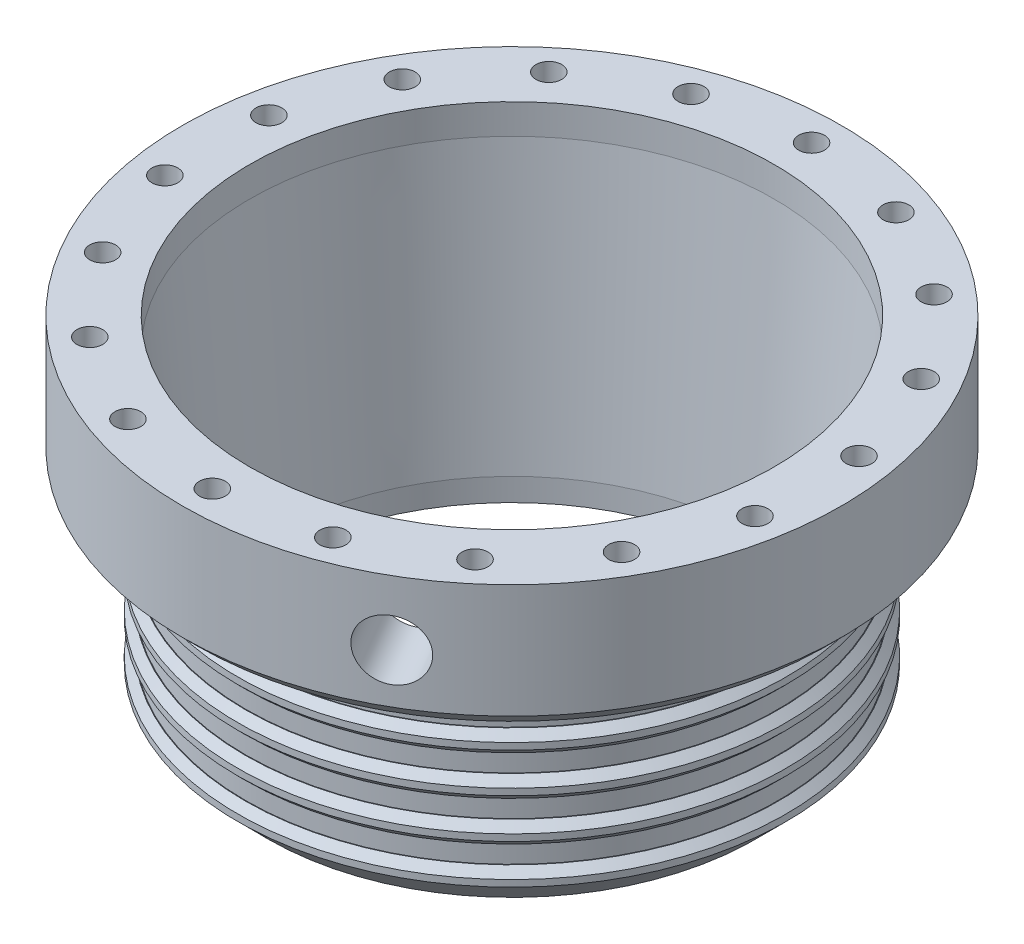
SolidWorks part; units mm, degrees
material "6061-T4 (SS)"
ref_plane "Front Plane" through (0, 0, 0) normal (0, 0, 1) x (1, 0, 0)
ref_plane "Top Plane" through (0, 0, 0) normal (0, 1, 0) x (1, 0, 0)
ref_plane "Right Plane" through (0, 0, 0) normal (1, 0, 0) x (0, 0, -1)
sketch "Sketch1" plane through (0, 0, 0) normal (0, 1, 0) x (1, 0, 0)
  circle A0 centre (0, 0) radius 55.5625
  circle A1 centre (0, 0) radius 58.1025
  dimension "D1" = 111.125
  dimension "D2" = 2.54
extrude "Boss-Extrude1" add sketch "Sketch1" along normal blind 38.1
sketch "Sketch2" plane through (0, 38.1, 0) normal (0, 1, 0) x (1, 0, 0)
  circle A0 centre (0, 0) radius 55.5625
  circle A1 centre (0, 0) radius 69.85
  circle A2 centre (0, 0) radius 55.5625 construction
  dimension "D1" = 139.7
extrude "Boss-Extrude2" add sketch "Sketch2" along normal blind 20.955
sketch "Sketch7" plane through (0, 0, 0) normal (0, 0, 1) x (1, 0, 0)
  line L0 (0, 0) -> (0, 88.9) construction
ref_plane "Plane1" through (0, 0, 0) normal (0.9659, 0, -0.2588) x (0, 1, 0)
ref_plane "Plane2" through (18.0785, 0, 67.4699) normal (0.2588, 0, 0.9659) x (0.9659, 0, -0.2588)
sketch "Sketch9" plane through (0, 0, 0) normal (0, 0, 1) x (1, 0, 0)
  line L0 (0, 0) -> (0, 88.9) construction
  line L2 (0, 0) -> (-58.1025, 0) construction
  line L3 (-58.1025, 0) -> (58.1025, 0) construction
  line L4 (-58.1025, 0) -> (-58.1025, 38.1) construction
  line L5 (-69.85, 38.1) -> (69.85, 38.1) construction
  line L6 (-58.1025, 38.1) -> (58.1025, 38.1) construction
  line L7 (-58.1025, 38.1) -> (-58.1025, 33.528)
  line L8 (-58.1025, 4.572) -> (-56.388, 4.572)
  line L9 (-58.1025, 4.572) -> (-58.1025, 8.382)
  line L10 (-58.1025, 8.382) -> (-56.388, 8.382)
  line L11 (-56.388, 4.572) -> (-56.388, 8.382)
  line L12 (-58.1025, 12.954) -> (-56.388, 12.954)
  line L13 (-58.1025, 12.954) -> (-58.1025, 16.764)
  line L14 (-58.1025, 16.764) -> (-56.388, 16.764)
  line L15 (-56.388, 12.954) -> (-56.388, 16.764)
  line L16 (-58.1025, 21.336) -> (-56.388, 21.336)
  line L17 (-58.1025, 21.336) -> (-58.1025, 25.146)
  line L18 (-58.1025, 25.146) -> (-56.388, 25.146)
  line L19 (-56.388, 21.336) -> (-56.388, 25.146)
  line L20 (-58.1025, 29.718) -> (-56.388, 29.718)
  line L21 (-58.1025, 29.718) -> (-58.1025, 33.528)
  line L22 (-58.1025, 33.528) -> (-56.388, 33.528)
  line L23 (-56.388, 29.718) -> (-56.388, 33.528)
  line L24 (-58.1025, 29.718) -> (-58.1025, 25.146)
  line L25 (-58.1025, 21.336) -> (-58.1025, 16.764)
  line L26 (-58.1025, 12.954) -> (-58.1025, 8.382)
  line L27 (-58.1025, 4.572) -> (-58.1025, 0)
  dimension "D1" = 58.1025
  dimension "D2" = 1.7145
  dimension "D3" = 3.81
revolve "Cut-Revolve1" cut sketch "Sketch9" angle 360 about L0
chamfer "Chamfer1" distance 1.5875 angle 45 1 edges at (0, 0, 58.1025)
sketch "Sketch10" plane through (0, 0, 0) normal (0, 0, 1) x (1, 0, 0)
  line L0 (0, 0) -> (0, 88.7441) construction
  line L1 (0, 0) -> (55.5625, 0) construction
  line L2 (55.5625, 0) -> (55.5625, 59.055)
  line L3 (55.5625, 59.055) -> (50.8, 0)
  line L4 (50.8, 0) -> (55.5625, 0)
  dimension "D1" = 55.5625
  dimension "D2" = 59.055
  dimension "D3" = 50.8
revolve "Revolve1" add sketch "Sketch10" angle 360 about L0
sketch "Sketch16" plane through (0, 59.055, 0) normal (0, 1, 0) x (1, 0, 0)
  circle A0 centre (0, 0) radius 69.85
  circle A1 centre (0, 0) radius 55.5625
  circle A3 centre (0, 0) radius 69.85 construction
  circle A5 centre (0, 0) radius 55.5625 construction
extrude "Boss-Extrude3" add sketch "Sketch16" along normal blind 6.35
sketch "Sketch11" plane through (0, 65.405, 0) normal (0, 1, 0) x (1, 0, 0)
  circle A0 centre (0, 0) radius 61.9633
  circle A1 centre (0, 0) radius 59.3217
  dimension "D1" = 123.9266
  dimension "D2" = 2.6416
sketch "Sketch12" plane through (0, 65.405, 0) normal (0, 1, 0) x (1, 0, 0)
  circle A0 centre (0, 0) radius 63.5 construction
  circle A1 centre (0, -63.5) radius 2.7432
  dimension "D1" = 5.4864
  dimension "D2" = 127
extrude "Cut-Extrude7" cut sketch "Sketch12" against normal blind 20.955 contours A1
pattern_circular "CirPattern2" count 18 over 360 about axis through (0, 0, 0) along (0, 1, 0) of "Cut-Extrude7"
sketch "Sketch13" plane through (0, 0, 0) normal (0, 0, 1) x (1, 0, 0)
  line L0 (0, 0) -> (50.8, 0) construction
  line L1 (0, 0) -> (0, 34.9502) construction
  line L2 (50.8, 0) -> (56.515, 0)
  line L3 (50.8, 0) -> (50.8, -5.715)
  line L4 (56.515, 0) -> (50.8, -5.715)
  dimension "D1" = 50.8
  dimension "D2" = 5.715
  dimension "D3" = 45
revolve "Revolve2" add sketch "Sketch13" angle 360 about L1
chamfer "Chamfer2" distance 1.27 angle 45 1 edges at (0, -5.715, -50.8)
sketch "Sketch14" plane through (0, 65.405, 0) normal (0, 1, 0) x (1, 0, 0)
  line L0 (0, -63.5) -> (54.9926, -31.75) construction
  line L1 (0, -35.9727) -> (0, 35.9727) construction
  line L2 (0, 0) -> (27.4963, -47.625) construction
  circle A1 centre (0, -63.5) radius 2.7432 construction
ref_plane "Plane3" through (27.4963, 0, 47.625) normal (0.5, 0, 0.866) x (0.866, 0, -0.5)
sketch "Sketch15" plane through (27.4963, 0, 47.625) normal (0.5, 0, 0.866) x (0.866, 0, -0.5)
  line L0 (0, 65.405) -> (0, 38.1) construction
  line L1 (-58.1025, 38.1) -> (58.1025, 38.1) construction
  circle A0 centre (0, 51.7525) radius 6.35
  dimension "D1" = 12.7
extrude "Cut-Extrude8" cut sketch "Sketch15" against normal up to next and the other way through all
chamfer "Chamfer3" distance 1.5875 angle 45 8 edges at (0, 33.528, -58.1025) (0, 29.718, -58.1025) (0, 21.336, -58.1025) (0, 25.146, -58.1025) (0, 12.954, -58.1025) (0, 16.764, -58.1025) (0, 8.382, -58.1025) (0, 4.572, -58.1025)
chamfer "Chamfer4" distance 3.175 angle 45 1 edges at (0, 38.1, 69.85)
